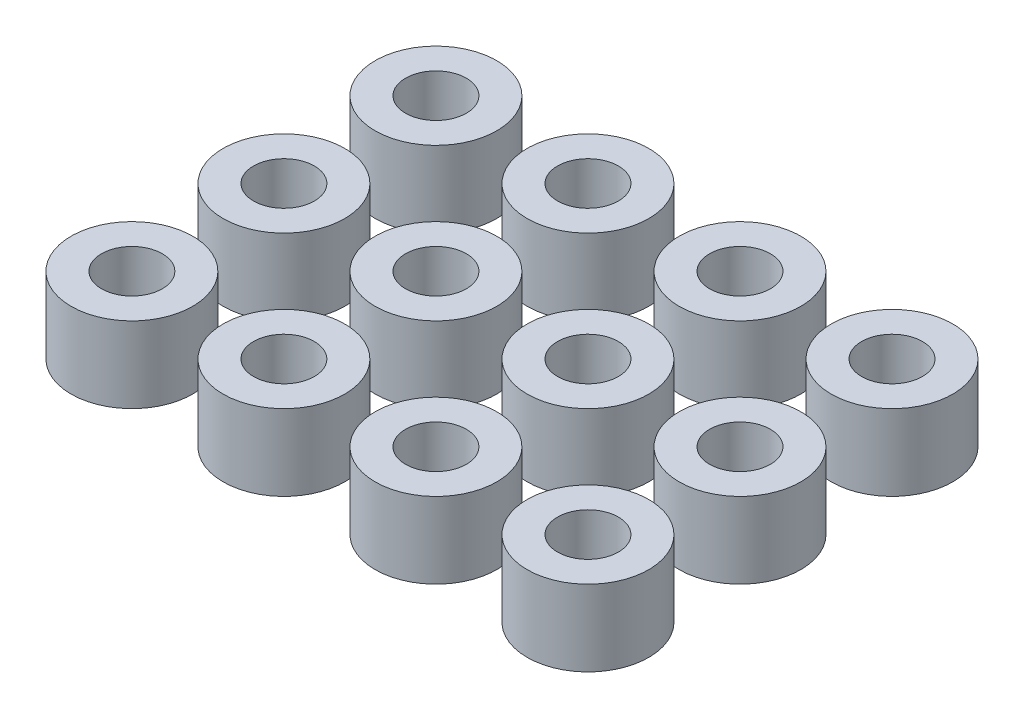
SolidWorks part; units mm, degrees
ref_plane "Plano frontal" through (0, 0, 0) normal (0, 0, 1) x (1, 0, 0)
ref_plane "Plano superior" through (0, 0, 0) normal (0, 1, 0) x (1, 0, 0)
ref_plane "Plano direito" through (0, 0, 0) normal (1, 0, 0) x (0, 0, -1)
sketch "Sketch1" plane through (0, 0, 0) normal (0, 1, 0) x (1, 0, 0)
  circle A0 centre (-15, -10) radius 2
  circle A1 centre (-15, -10) radius 4
  circle A2 centre (-5, -10) radius 2
  circle A3 centre (-5, -10) radius 4
  circle A4 centre (5, -10) radius 2
  circle A5 centre (5, -10) radius 4
  circle A6 centre (15, -10) radius 2
  circle A7 centre (15, -10) radius 4
  circle A8 centre (-5, 0) radius 2
  circle A9 centre (-5, 0) radius 4
  circle A10 centre (5, 0) radius 2
  circle A11 centre (5, 0) radius 4
  circle A12 centre (15, 0) radius 2
  circle A13 centre (15, 0) radius 4
  circle A14 centre (-5, 10) radius 2
  circle A15 centre (-5, 10) radius 4
  circle A16 centre (5, 10) radius 2
  circle A17 centre (5, 10) radius 4
  circle A18 centre (15, 10) radius 2
  circle A19 centre (15, 10) radius 4
  circle A20 centre (-15, 0) radius 2
  circle A21 centre (-15, 0) radius 4
  circle A22 centre (-15, 10) radius 2
  circle A23 centre (-15, 10) radius 4
  dimension "D1" = 8
  dimension "D2" = 4
  dimension "D5" = 15
  dimension "D6" = 10
  dimension "D3" = 4
  dimension "D4" = 3
extrude "Boss-Extrude1" add sketch "Sketch1" along normal blind 5
